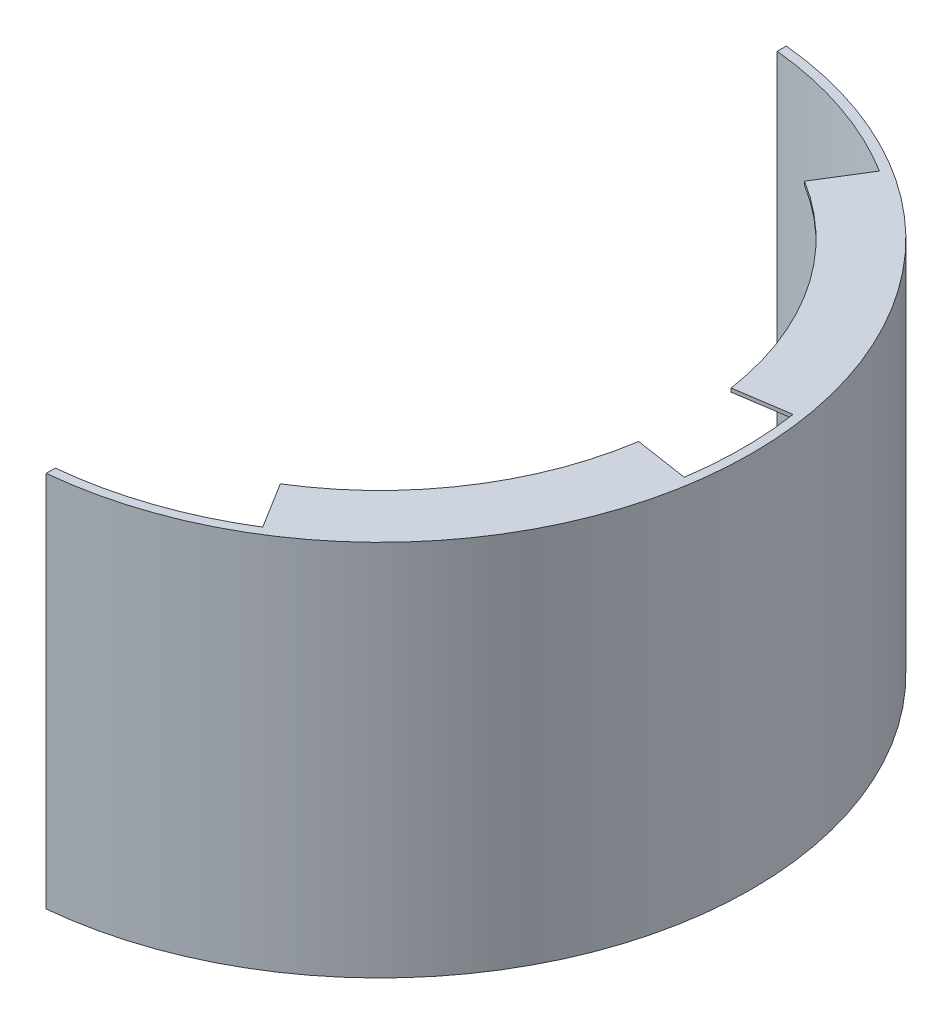
SolidWorks part; units mm, degrees
material "PLA"
ref_plane "Front Plane" through (0, 0, 0) normal (0, 0, 1) x (1, 0, 0)
ref_plane "Top Plane" through (0, 0, 0) normal (0, 1, 0) x (1, 0, 0)
ref_plane "Right Plane" through (0, 0, 0) normal (1, 0, 0) x (0, 0, -1)
sketch "Sketch1" plane through (0, 0, 0) normal (0, 1, 0) x (1, 0, 0)
  line L2 (20, 204.0221) -> (20, 198.9975)
  line L3 (20, -198.9975) -> (20, -204.0221)
  arc A0 (20, -204.0221) -> (20, 204.0221) centre (0, 0) ccw
  arc A1 (20, -198.9975) -> (20, 198.9975) centre (0, 0) ccw
  dimension "D1" = 410
  dimension "D2" = 400
  dimension "D3" = 20
extrude "Boss-Extrude1" add sketch "Sketch1" along normal blind 208
sketch "Sketch2" plane through (0, 0, 0) normal (0, 1, 0) x (1, 0, 0)
  line L0 (105.3565, -170) -> (89.5531, -144.5)
  line L1 (197.7372, -30) -> (168.0766, -25.5)
  line L2 (197.7372, 30) -> (168.0766, 25.5)
  line L3 (105.3565, 170) -> (89.5531, 144.5)
  line L4 (-194.4119, 0) -> (395.578, 0) construction
  arc A0 (89.5531, -144.5) -> (168.0766, -25.5) centre (0, 0) ccw
  arc A1 (20, -198.9975) -> (20, 198.9975) centre (0, 0) ccw construction
  arc A2 (105.3565, -170) -> (197.7372, -30) centre (0, 0) ccw
  arc A3 (168.0766, 25.5) -> (89.5531, 144.5) centre (0, 0) ccw
  arc A4 (197.7372, 30) -> (105.3565, 170) centre (0, 0) ccw
  dimension "D1" = 30
  dimension "D3" = 30
  dimension "D2" = 140
  dimension "D4" = 30
  dimension "D5" = 30
  dimension "D6" = 140
extrude "Boss-Extrude2" add sketch "Sketch2" along normal blind 2
ref_plane "Plane1" through (0, 104, 0) normal (0, 1, 0) x (1, 0, 0)
mirror "Mirror1" about plane through (0, 104, 0) normal (0, 1, 0) of "Boss-Extrude2"
